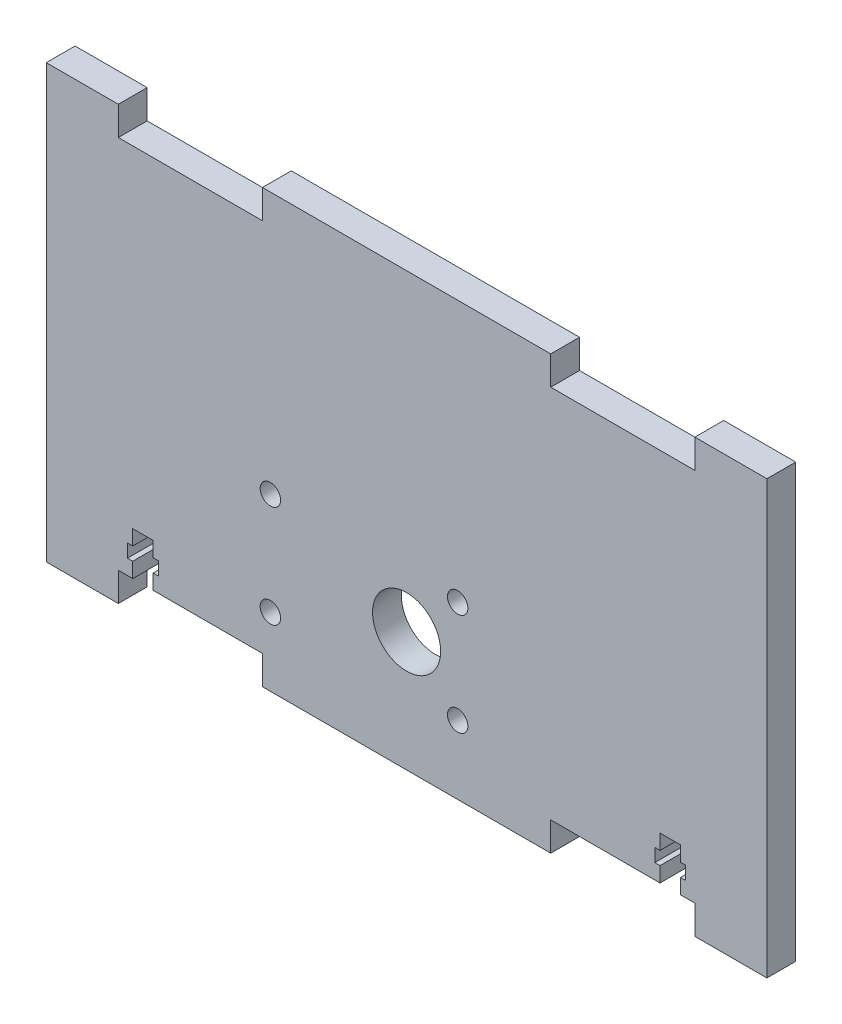
SolidWorks part; units mm, degrees
ref_plane "Front Plane" through (0, 0, 0) normal (0, 0, 1) x (1, 0, 0)
ref_plane "Top Plane" through (0, 0, 0) normal (0, 1, 0) x (1, 0, 0)
ref_plane "Right Plane" through (0, 0, 0) normal (1, 0, 0) x (0, 0, -1)
sketch "Sketch1" plane through (0, 0, 0) normal (0, 0, 1) x (1, 0, 0)
  line L1 (0, 0) -> (127, 0)
  line L2 (0, 0) -> (0, 76.2)
  line L3 (0, 76.2) -> (127, 76.2)
  line L4 (127, 0) -> (127, 76.2)
  dimension "D1" = 127
  dimension "D2" = 76.2
extrude "Boss-Extrude1" add sketch "Sketch1" along normal blind 5.08
sketch "Sketch2" plane through (0, 0, 5.08) normal (0, 0, 1) x (1, 0, 0)
  line L0 (0, 0) -> (127, 0) construction
  line L1 (12.7, 0) -> (38.1, 0)
  line L2 (12.7, 0) -> (12.7, 5.08)
  line L3 (12.7, 5.08) -> (38.1, 5.08)
  line L4 (38.1, 0) -> (38.1, 5.08)
  line L5 (12.7, 5.08) -> (0, 5.08) construction
  line L6 (88.9, 0) -> (114.3, 0)
  line L7 (88.9, 0) -> (88.9, 5.08)
  line L8 (88.9, 5.08) -> (114.3, 5.08)
  line L9 (114.3, 0) -> (114.3, 5.08)
  line L10 (0, 76.2) -> (0, 0) construction
  line L11 (38.1, 5.08) -> (88.9, 5.08) construction
  line L12 (114.3, 5.08) -> (127, 5.08) construction
  line L13 (127, 0) -> (127, 76.2) construction
  dimension "D1" = 5.08
  dimension "D2" = 12.7
  dimension "D3" = 50.8
extrude "Cut-Extrude1" cut sketch "Sketch2" against normal up to next
sketch "Sketch3" plane through (0, 0, 5.08) normal (0, 0, 1) x (1, 0, 0)
  line L1 (0, 76.2) -> (0, 0) construction
  line L5 (127, 0) -> (127, 76.2) construction
  line L6 (0, 5.08) -> (0, 71.12)
  line L9 (127, 71.12) -> (127, 5.08)
  line L10 (0, 5.08) -> (127, 5.08) construction
  line L12 (12.7, 5.08) -> (0, 5.08) construction
  line L13 (0, 5.08) -> (0, 71.12)
  line L14 (38.1, 76.2) -> (88.9, 76.2)
  line L15 (38.1, 76.2) -> (38.1, 71.12)
  line L17 (114.3, 71.12) -> (127, 71.12) construction
  line L18 (0, 71.12) -> (12.7, 71.12) construction
  line L19 (12.7, 71.12) -> (114.3, 71.12) construction
  line L20 (127, 76.2) -> (0, 76.2) construction
  line L21 (12.7, 71.12) -> (12.7, 76.2)
  line L22 (12.7, 76.2) -> (0, 76.2)
  line L23 (0, 76.2) -> (0, 71.12)
  line L24 (114.3, 71.12) -> (114.3, 76.2)
  line L25 (114.3, 76.2) -> (127, 76.2)
  line L26 (127, 76.2) -> (127, 71.12)
  line L27 (38.1, 71.12) -> (88.9, 71.12)
  line L28 (88.9, 76.2) -> (88.9, 71.12)
  line L29 (12.7, 71.12) -> (38.1, 71.12)
  line L30 (12.7, 71.12) -> (12.7, 76.2)
  line L31 (12.7, 76.2) -> (38.1, 76.2)
  line L32 (38.1, 71.12) -> (38.1, 76.2)
  line L33 (88.9, 71.12) -> (114.3, 71.12)
  line L34 (88.9, 71.12) -> (88.9, 76.2)
  line L35 (88.9, 76.2) -> (114.3, 76.2)
  line L36 (114.3, 71.12) -> (114.3, 76.2)
  line M20 (127, 76.2) -> (0, 76.2)
  dimension "D1" = 5.08
  dimension "D2" = 101.6
  dimension "D3" = 25.4
  dimension "D4" = 25.4
extrude "Cut-Extrude2" cut sketch "Sketch3" against normal through all contours L21 L29 L15 M20 | L28 L33 L24 M20
sketch "Sketch4" plane through (0, 0, 5.08) normal (0, 0, 1) x (1, 0, 0)
  circle A0 centre (63.5, 21.08) radius 6 construction
  circle A1 centre (63.5, 21.08) radius 6
extrude "Cut-Extrude3" cut sketch "Sketch4" against normal up to next
sketch "Sketch5" plane through (0, 0, 5.08) normal (0, 0, 1) x (1, 0, 0)
  circle A0 centre (72.5, 30.08) radius 3.7 construction
  circle A1 centre (72.5, 12.08) radius 3.7 construction
  circle A2 centre (39.5, 12.08) radius 3.7 construction
  circle A3 centre (39.5, 30.08) radius 3.7 construction
  circle A4 centre (72.5, 30.08) radius 3.7
  circle A5 centre (72.5, 12.08) radius 3.7
  circle A6 centre (39.5, 12.08) radius 3.7
  circle A7 centre (39.5, 30.08) radius 3.7
sketch "Sketch8" plane through (0, 0, 5.08) normal (0, 0, 1) x (1, 0, 0)
  line L0 (18.84, 5.08) -> (15.24, 5.08) construction
  line L3 (15.24, 5.08) -> (15.24, 12.7)
  line L4 (15.24, 12.7) -> (18.84, 12.7)
  line L5 (18.84, 12.7) -> (18.84, 5.08)
  line L6 (18.84, 5.08) -> (15.24, 5.08)
  dimension "D1" = 7.62
extrude "Cut-Extrude6" cut sketch "Sketch8" against normal up to next (5.08 mm away)
sketch "Sketch9" plane through (0, 0, 5.08) normal (0, 0, 1) x (1, 0, 0)
  line L0 (18.84, 8.89) -> (19.7641, 8.89) construction
  line L1 (14.3158, 10.052) -> (19.7641, 10.052)
  line L2 (14.3158, 10.052) -> (14.3158, 7.7279)
  line L3 (14.3158, 7.7279) -> (19.7641, 7.7279)
  line L4 (19.7641, 10.052) -> (19.7641, 7.7279)
  line L5 (18.84, 5.08) -> (18.84, 12.7) construction
  line L6 (15.24, 8.89) -> (14.3158, 8.89) construction
  line L7 (15.24, 12.7) -> (15.24, 5.08) construction
  dimension "D1" = 5.4483
  dimension "D2" = 2.3241
extrude "Cut-Extrude7" cut sketch "Sketch9" against normal up to next (5.08 mm away)
ref_plane "Plane1" through (63.5, 0, 0) normal (-1, 0, 0) x (0, 0, 1)
mirror "Mirror1" about plane through (63.5, 0, 0) normal (-1, 0, 0) of "Cut-Extrude6", "Cut-Extrude7"
hole_wizard "M3 Clearance Hole1" positions "Sketch11" profile "Sketch12" hole size "M3" standard "ISO" end condition up to next
sketch "Sketch11" plane through (0, 0, 5.08) normal (0, 0, 1) x (1, 0, 0)
  point P0 (39.5, 30.08)
  point P3 (72.5, 30.08)
  point P6 (72.5, 12.08)
  point P9 (39.5, 12.08)
sketch "Sketch12" plane through (39.5, 30.08, 5.08) normal (1, 0, 0) x (0, -1, 0)
  line L0 (0, 0) -> (0, 5.08)
  line L1 (0, 5.08) -> (1.8, 5.08)
  line L2 (1.8, 5.08) -> (1.8, 0)
  line L5 (1.8, 0) -> (0, 0)
  line L11 (0, -6.35) -> (0, 107.95) construction
  dimension "Thru Hole Dia." = 3.6
  dimension "Thru Hole Depth" = 5.08
equation "\"Foamcore\"= 0.2in"
equation "\"MDF\"= 0.2in"
equation "\"D1@Boss-Extrude1\"=\"MDF\""
equation "\"D1@Sketch2\"=\"MDF\""
equation "\"D1@Sketch3\"=\"MDF\""
equation "\"NutD\"= 0.2145in"
equation "\"NutH\"= 0.0915in"
equation "\"D1@Sketch9\"=\"NutD\""
equation "\"D2@Sketch9\"=\"NutH\""
equation "\"TubeR\"= 0.8in"
equation "\"MountScrewL\"= 0.3in"
equation "\"D1@Sketch8\"=\"MountScrewL\""
equation "\"MountScrewD\"= 3.6mm"
